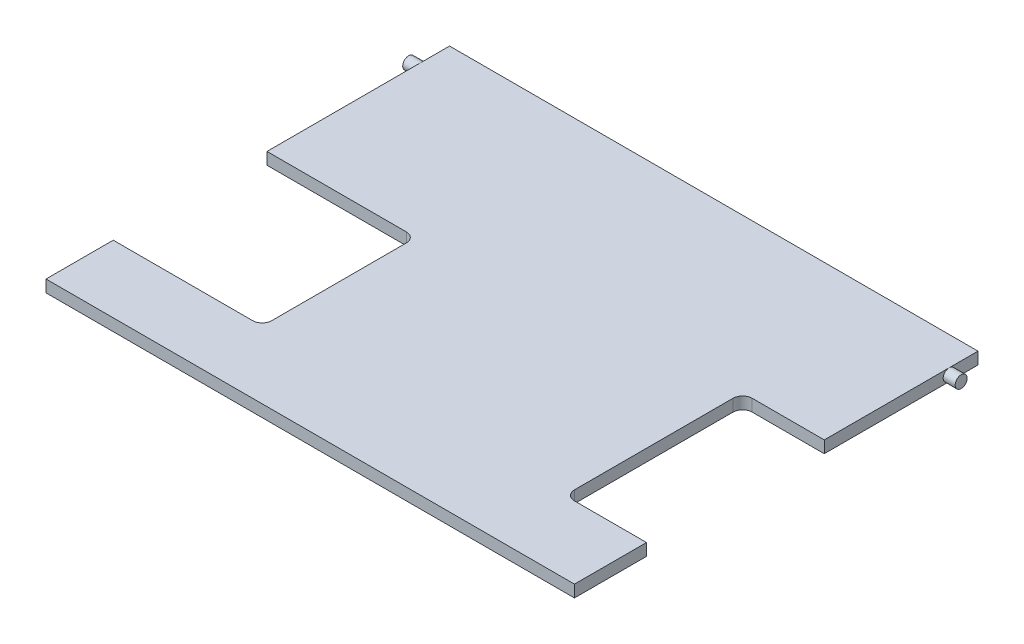
SolidWorks part; units mm, degrees
ref_plane "Alzado" through (0, 0, 0) normal (0, 0, 1) x (1, 0, 0)
ref_plane "Planta" through (0, 0, 0) normal (0, 1, 0) x (1, 0, 0)
ref_plane "Vista lateral" through (0, 0, 0) normal (1, 0, 0) x (0, 0, -1)
sketch "Croquis1" plane through (0, 0, 0) normal (0, 1, 0) x (1, 0, 0)
  line L1 (0, 0) -> (-110, 0)
  line L2 (0, 0) -> (0, 84)
  line L3 (0, 84) -> (-110, 84)
  line L4 (-110, 0) -> (-110, 84)
  dimension "D1" = 84
  dimension "D2" = 110
extrude "Saliente-Extruir1" add sketch "Croquis1" along normal blind 2.5
sketch "Croquis2" plane through (0, 0, 0) normal (1, 0, 0) x (0, 0, -1)
  line L0 (84, 1.25) -> (78, 1.25) construction
  line L1 (84, 2.5) -> (84, 0) construction
  circle A0 centre (78, 1.25) radius 1.25
  dimension "D1" = 6
extrude "Saliente-Extruir2" add sketch "Croquis2" along normal blind 2.5
sketch "Croquis3" plane through (-110, 0, 0) normal (-1, 0, 0) x (0, 0, 1)
  line L0 (-84, 1.25) -> (-78, 1.25) construction
  line L2 (-84, 2.5) -> (-84, 0) construction
  circle A0 centre (-78, 1.25) radius 1.25
  dimension "D1" = 6
extrude "Saliente-Extruir3" add sketch "Croquis3" along normal blind 2.5
sketch "Croquis4" plane through (0, 2.5, 0) normal (0, 1, 0) x (1, 0, 0)
  line L0 (-110, 0) -> (-104, 0) construction
  line L1 (-110, 0) -> (0, 0) construction
  line L2 (-104, 0) -> (-104, 14) construction
  line L3 (-81, 46) -> (-110, 46)
  line L4 (-79, 16) -> (-79, 44)
  line L5 (-110, 78) -> (-110, 0) construction
  line L6 (-81, 14) -> (-110, 14)
  line L7 (0, 0) -> (-17, 0) construction
  line L8 (-17, 0) -> (-17, 15) construction
  line L9 (-17, 17) -> (-17, 50)
  line L10 (-15, 52) -> (0, 52)
  line L11 (0, 0) -> (0, 78) construction
  line L12 (-15, 15) -> (0, 15)
  line L13 (0, 52) -> (0, 15)
  line L14 (-110, 46) -> (-110, 14)
  arc A0 (-79, 44) -> (-81, 46) centre (-81, 44) ccw
  arc A1 (-81, 14) -> (-79, 16) centre (-81, 16) ccw
  arc A2 (-15, 15) -> (-17, 17) centre (-15, 17) cw
  arc A3 (-17, 50) -> (-15, 52) centre (-15, 50) cw
  point P14 (-79, 46)
  point P17 (-79, 14)
  point P32 (-17, 52)
  dimension "D5" = 2
  dimension "D9" = 2
  dimension "D1" = 6
  dimension "D2" = 14
  dimension "D3" = 25
  dimension "D4" = 32
  dimension "D6" = 17
  dimension "D7" = 15
  dimension "D8" = 37
extrude "Cortar-Extruir1" cut sketch "Croquis4" against normal blind 10
